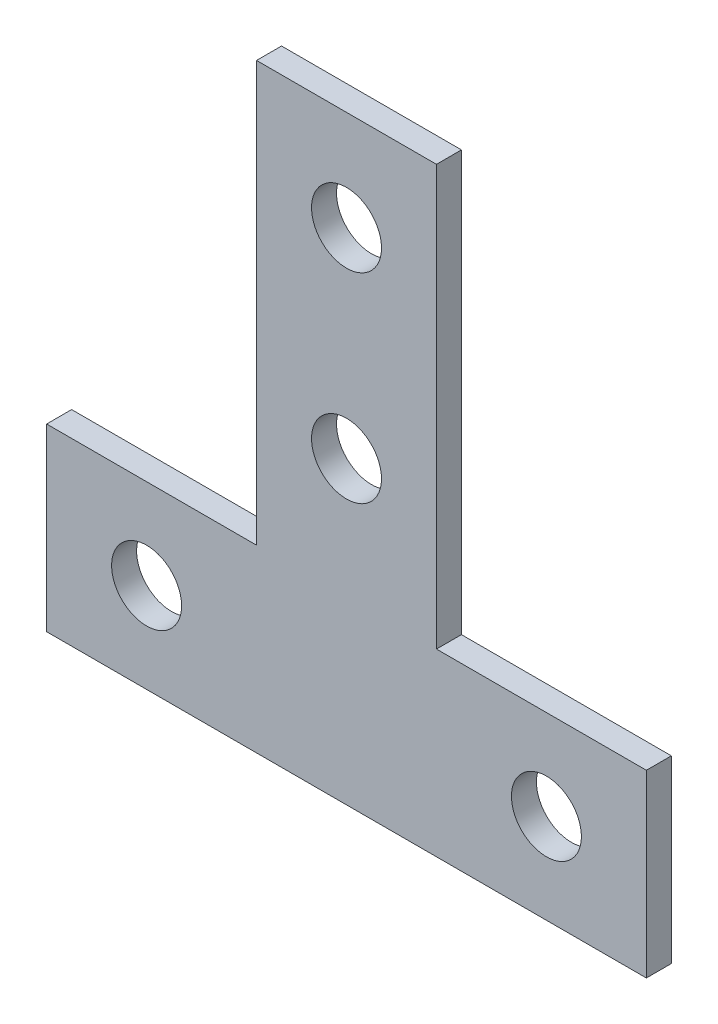
SolidWorks part; units mm, degrees
ref_plane "Спереди" through (0, 0, 0) normal (0, 0, 1) x (1, 0, 0)
ref_plane "Сверху" through (0, 0, 0) normal (0, 1, 0) x (1, 0, 0)
ref_plane "Справа" through (0, 0, 0) normal (1, 0, 0) x (0, 0, -1)
sketch "Эскиз1" plane through (0, 0, 0) normal (0, 0, 1) x (1, 0, 0)
  line L0 (-30, 0) -> (30, 0)
  line L1 (-30, 0) -> (-30, 18)
  line L2 (-30, 18) -> (-9, 18)
  line L3 (-9, 18) -> (-9, 60)
  line L4 (-9, 60) -> (9, 60)
  line L5 (9, 60) -> (9, 18)
  line L6 (9, 18) -> (30, 18)
  line L7 (30, 18) -> (30, 0)
  line L8 (-20, 9) -> (20, 9) construction
  circle A0 centre (0, 50) radius 3.5
  circle A1 centre (0, 30) radius 3.5
  circle A2 centre (-20, 9) radius 3.5
  circle A3 centre (20, 9) radius 3.5
  point P4 (0, 0)
  point P18 (0, 9)
  point P19 (30, 9)
  dimension "D5" = 10
  dimension "D6" = 20
  dimension "D7" = 7
  dimension "D1" = 60
  dimension "D2" = 60
  dimension "D3" = 18
  dimension "D4" = 40
extrude "Бобышка-Вытянуть1" add sketch "Эскиз1" along normal blind 2.5
